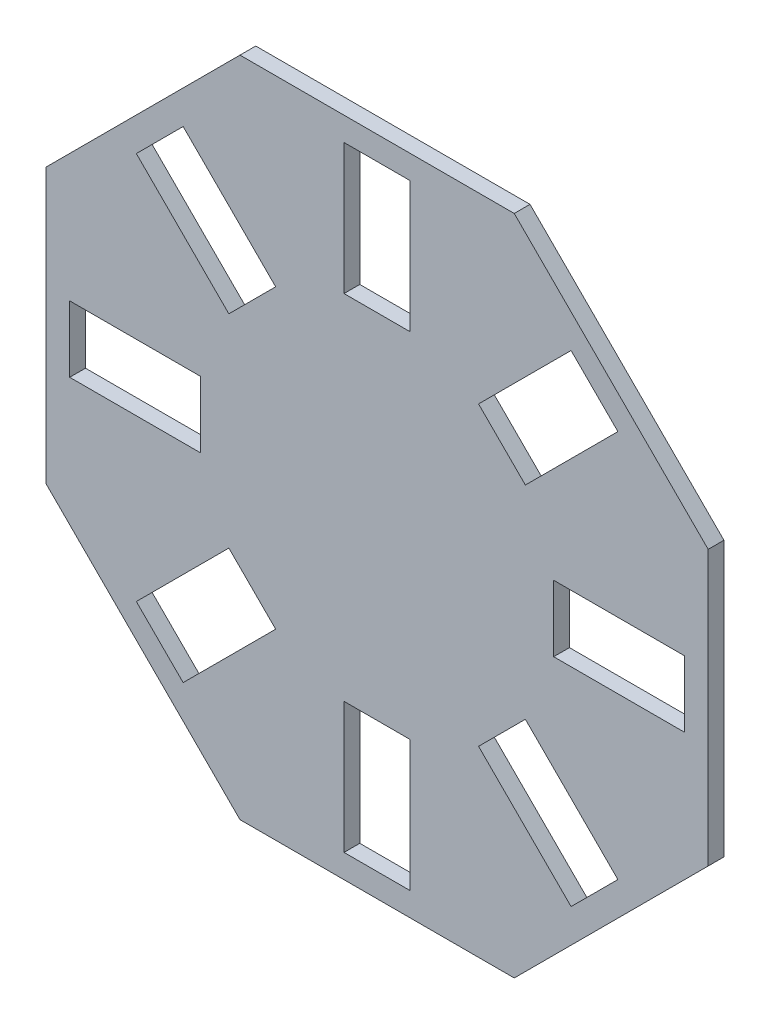
SolidWorks part; units mm, degrees
ref_plane "Front Plane" through (0, 0, 0) normal (0, 0, 1) x (1, 0, 0)
ref_plane "Top Plane" through (0, 0, 0) normal (0, 1, 0) x (1, 0, 0)
ref_plane "Right Plane" through (0, 0, 0) normal (1, 0, 0) x (0, 0, -1)
sketch "Sketch1" plane through (0, 0, 0) normal (0, 0, 1) x (1, 0, 0)
  line L0 (47.0226, -32.1734) -> (76.3675, -61.5183)
  line L9 (105, 43.4924) -> (43.4924, 105)
  line L10 (43.4924, 105) -> (-43.4924, 105)
  line L11 (-43.4924, 105) -> (-105, 43.4924)
  line L12 (-105, 43.4924) -> (-105, -43.4924)
  line L13 (-105, -43.4924) -> (-43.4924, -105)
  line L14 (-43.4924, -105) -> (43.4924, -105)
  line L15 (43.4924, -105) -> (105, -43.4924)
  line L16 (105, -43.4924) -> (105, 43.4924)
  line L17 (56, -10.5) -> (97.5, -10.5)
  line L18 (56, -10.5) -> (56, 10.5)
  line L19 (56, 10.5) -> (97.5, 10.5)
  line L20 (97.5, -10.5) -> (97.5, 10.5)
  line L21 (32.1734, -47.0226) -> (47.0226, -32.1734)
  line L22 (32.1734, -47.0226) -> (61.5183, -76.3675)
  line L23 (61.5183, -76.3675) -> (76.3675, -61.5183)
  line L24 (10.5, -56) -> (10.5, -97.5)
  line L25 (-10.5, -56) -> (10.5, -56)
  line L26 (-10.5, -56) -> (-10.5, -97.5)
  line L27 (-10.5, -97.5) -> (10.5, -97.5)
  line L28 (-32.1734, -47.0226) -> (-61.5183, -76.3675)
  line L29 (-47.0226, -32.1734) -> (-32.1734, -47.0226)
  line L30 (-47.0226, -32.1734) -> (-76.3675, -61.5183)
  line L31 (-76.3675, -61.5183) -> (-61.5183, -76.3675)
  line L32 (-56, -10.5) -> (-97.5, -10.5)
  line L33 (-56, 10.5) -> (-56, -10.5)
  line L34 (-56, 10.5) -> (-97.5, 10.5)
  line L35 (-97.5, 10.5) -> (-97.5, -10.5)
  line L36 (-47.0226, 32.1734) -> (-76.3675, 61.5183)
  line L37 (-32.1734, 47.0226) -> (-47.0226, 32.1734)
  line L38 (-32.1734, 47.0226) -> (-61.5183, 76.3675)
  line L39 (-61.5183, 76.3675) -> (-76.3675, 61.5183)
  line L40 (-10.5, 56) -> (-10.5, 97.5)
  line L41 (10.5, 56) -> (-10.5, 56)
  line L42 (10.5, 56) -> (10.5, 97.5)
  line L43 (10.5, 97.5) -> (-10.5, 97.5)
  line L44 (32.1734, 47.0226) -> (61.5183, 76.3675)
  line L45 (47.0226, 32.1734) -> (32.1734, 47.0226)
  line L46 (47.0226, 32.1734) -> (76.3675, 61.5183)
  line L47 (76.3675, 61.5183) -> (61.5183, 76.3675)
  circle A0 centre (0, 0) radius 105 construction
  point P45 (0, 0)
  dimension "D1" = 7.5
  dimension "D2" = 41.5
  dimension "D3" = 21
  dimension "D4" = 10.5
  dimension "D5" = 8
extrude "Boss-Extrude1" add sketch "Sketch1" along normal blind 5
